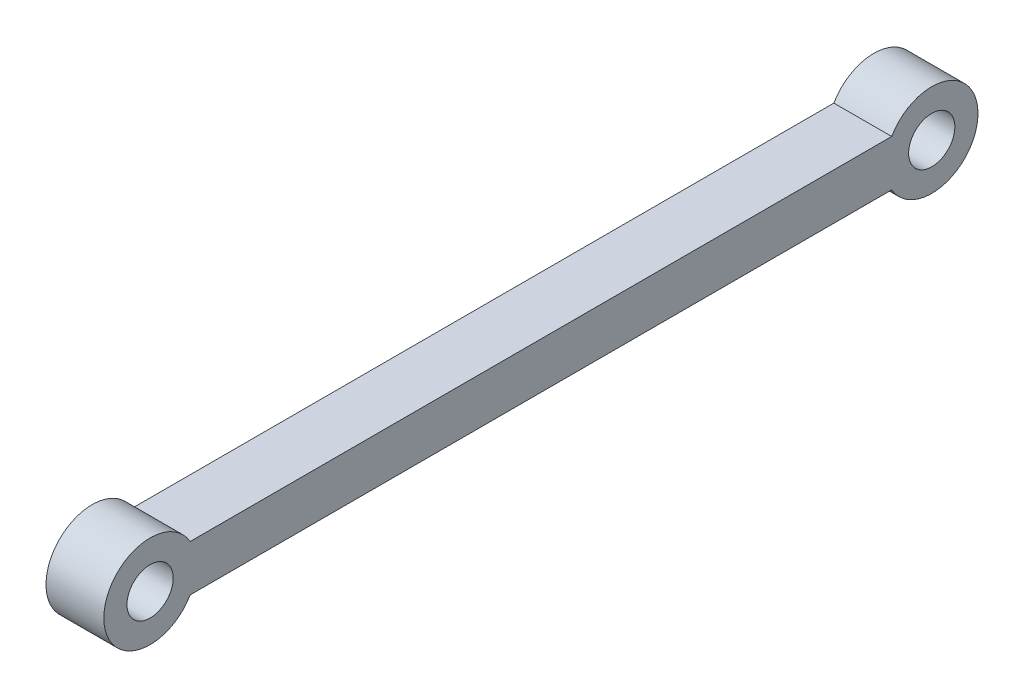
SolidWorks part; units mm, degrees
ref_plane "Front Plane" through (0, 0, 0) normal (0, 0, 1) x (1, 0, 0)
ref_plane "Top Plane" through (0, 0, 0) normal (0, 1, 0) x (1, 0, 0)
ref_plane "Right Plane" through (0, 0, 0) normal (1, 0, 0) x (0, 0, -1)
sketch "Sketch1" plane through (0, 0, 0) normal (1, 0, 0) x (0, 0, -1)
  line L1 (-15.1629, -2) -> (15.1629, -2)
  line L3 (-15.1629, 0) -> (15.1629, 0)
  arc A0 (-15.1629, 0) -> (-15.1629, -2) centre (-16.895, -1) ccw
  arc A1 (15.1629, -2) -> (15.1629, 0) centre (16.895, -1) ccw
  circle A2 centre (-16.895, -1) radius 1
  circle A3 centre (16.895, -1) radius 1
  point P0 (0, 0)
  point P1 (0, 0)
  point P3 (0, -2)
  dimension "D2" = 4
  dimension "D4" = 2
  dimension "D3" = 2
  dimension "D1" = 33.79
extrude "Boss-Extrude1" add sketch "Sketch1" along normal mid plane 2.5
